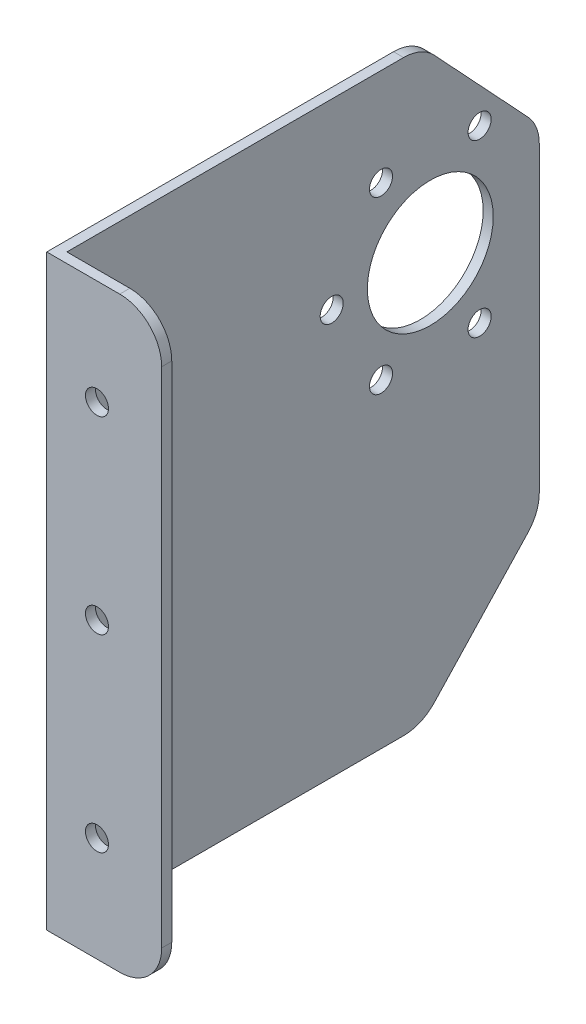
SolidWorks part; units mm, degrees
ref_plane "Front Plane" through (0, 0, 0) normal (0, 0, 1) x (1, 0, 0)
ref_plane "Top Plane" through (0, 0, 0) normal (0, 1, 0) x (1, 0, 0)
ref_plane "Right Plane" through (0, 0, 0) normal (1, 0, 0) x (0, 0, -1)
sketch "Sketch1" plane through (0, 0, 0) normal (1, 0, 0) x (0, 0, -1)
  line L1 (0, 0) -> (115, 0)
  line L2 (0, 0) -> (0, -140)
  line L3 (0, -140) -> (115, -140)
  line L4 (115, 0) -> (115, -140)
  dimension "D1" = 115
  dimension "D2" = 140
extrude "Boss-Extrude1" add sketch "Sketch1" along normal blind 2.4
sketch "Sketch2" plane through (2.4, 0, 0) normal (1, 0, 0) x (0, 0, -1)
  line L0 (87, 0) -> (115, -30)
  line L1 (115, 0) -> (0, 0) construction
  line L2 (115, -140) -> (115, 0) construction
  line L3 (115, -30) -> (142.6162, -32.5054)
  line L4 (142.6162, -32.5054) -> (142.6162, 14.8756)
  line L5 (142.6162, 14.8756) -> (87, 0)
  line L6 (115, -110) -> (87, -140)
  line L7 (0, -140) -> (115, -140) construction
  line L8 (87, -140) -> (87, -152.6611)
  line L9 (87, -152.6611) -> (136.31, -152.6611)
  line L10 (136.31, -152.6611) -> (115, -110)
  line L12 (0, 0) -> (0, -140) construction
  dimension "D1" = 30
  dimension "D2" = 87
  dimension "D3" = 87
  dimension "D4" = 30
extrude "Cut-Extrude1" cut sketch "Sketch2" against normal through all
fillet "Fillet1" radius 10 4 edges at (1.2, -140, -87) (1.2, -110, -115) (1.2, -30, -115) (1.2, 0, -87)
sketch "Sketch3" plane through (2.4, 0, 0) normal (1, 0, 0) x (0, 0, -1)
  line L0 (82.6545, 0) -> (0, 0) construction
  line L1 (0, -140) -> (2.4, -140)
  line L2 (0, -140) -> (0, 0)
  line L3 (0, 0) -> (2.4, 0)
  line L4 (2.4, -140) -> (2.4, 0)
  dimension "D1" = 2.4
extrude "Boss-Extrude2" add sketch "Sketch3" along normal blind 25
fillet "Fillet2" radius 10 2 edges at (27.4, -140, -1.2) (27.4, 0, -1.2)
sketch "Sketch4" plane through (0, 0, 0) normal (0, 0, 1) x (1, 0, 0)
  line L0 (17.4, 0) -> (0, 0) construction
  line L1 (17.4, -140) -> (0, -140) construction
  line L2 (27.4, -10) -> (27.4, -130) construction
  circle A0 centre (11.975, -70) radius 2.75
  circle A1 centre (11.975, -25) radius 2.75
  circle A2 centre (11.975, -115) radius 2.75
  point P12 (27.4, -70)
  dimension "D1" = 5.5
  dimension "D2" = 5.5
  dimension "D3" = 5.5
  dimension "D4" = 25
  dimension "D5" = 25
extrude "Cut-Extrude2" cut sketch "Sketch4" against normal through all
sketch "Sketch5" plane through (2.4, 0, 0) normal (1, 0, 0) x (0, 0, -1)
  circle A0 centre (89.0279, -43.506) radius 15
  circle A1 centre (77.2779, -23.1544) radius 2.75 construction
  circle A3 centre (100.7779, -23.1544) radius 2.75 construction
  circle A4 centre (77.2779, -23.1544) radius 2.75
  circle A6 centre (100.7779, -23.1544) radius 2.75
  circle A7 centre (65.5279, -43.506) radius 2.75 construction
  circle A8 centre (77.2779, -63.8576) radius 2.75 construction
  circle A9 centre (65.5279, -43.506) radius 2.75
  circle A10 centre (77.2779, -63.8576) radius 2.75
  circle A11 centre (100.7779, -63.8576) radius 2.75 construction
  circle A12 centre (100.7779, -63.8576) radius 2.75
  point P2 (89.0279, -43.506)
  dimension "D1" = 30
extrude "Cut-Extrude3" cut sketch "Sketch5" against normal through all
